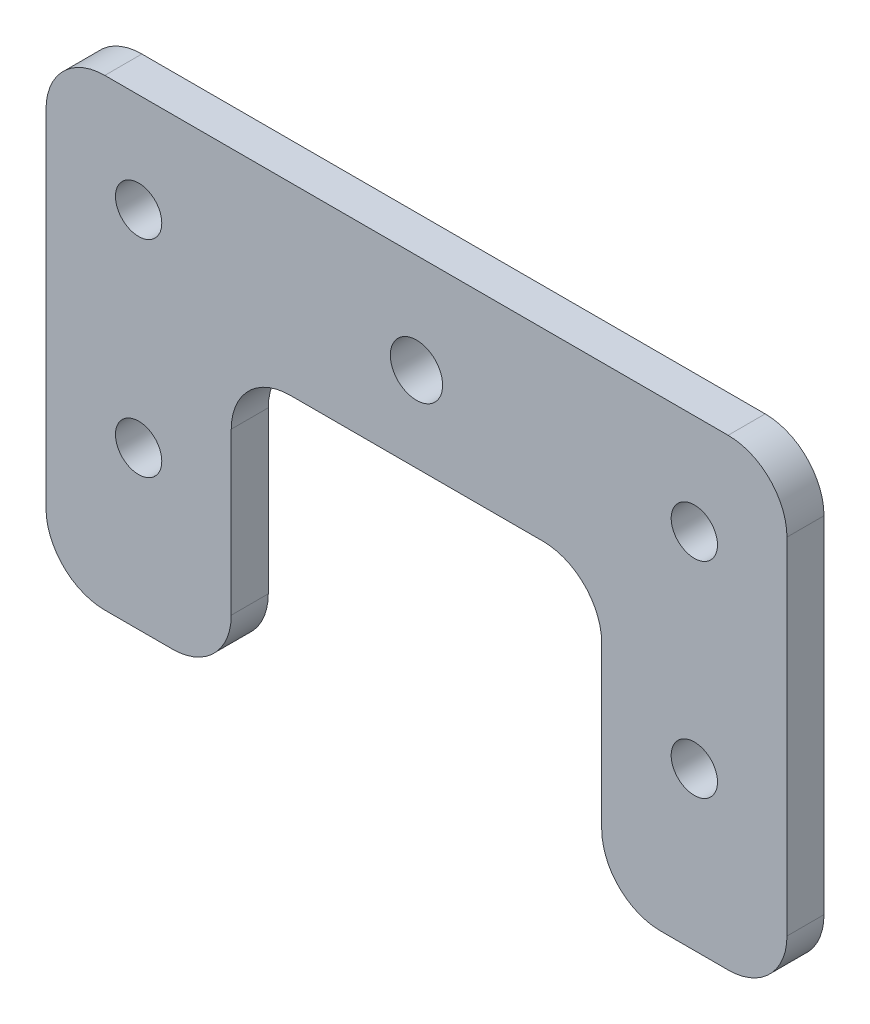
SolidWorks part; units mm, degrees
ref_plane "Alzado" through (0, 0, 0) normal (0, 0, 1) x (1, 0, 0)
ref_plane "Planta" through (0, 0, 0) normal (0, 1, 0) x (1, 0, 0)
ref_plane "Vista lateral" through (0, 0, 0) normal (1, 0, 0) x (0, 0, -1)
sketch "Croquis1" plane through (0, 0, 0) normal (0, 0, 1) x (1, 0, 0)
  line L1 (26.5381, 6.6994) -> (53.8381, 6.6994)
  line L2 (0.1881, 6.6044) -> (0.1881, 20.2544)
  line L3 (6.5381, 26.6044) -> (73.8381, 26.6044)
  line L4 (80.1881, 6.6044) -> (80.1881, 20.2544)
  line L6 (0.1881, 6.6044) -> (0.1881, -17.0456)
  line L7 (6.5381, -23.3956) -> (13.8381, -23.3956)
  line L8 (20.1881, 0.3494) -> (20.1881, -17.0456)
  line L13 (40.1881, 26.6044) -> (40.1881, -35.7819) construction
  line L14 (73.8381, -23.3956) -> (66.5381, -23.3956)
  line L15 (60.1881, 0.3494) -> (60.1881, -17.0456)
  line L16 (80.1881, 6.6044) -> (80.1881, -17.0456)
  circle A1 centre (10.1881, 15.8665) radius 2.5
  circle A2 centre (70.1881, 15.7714) radius 2.5
  circle A3 centre (10.1881, -6.3956) radius 2.5
  arc A5 (26.5381, 6.6994) -> (20.1881, 0.3494) centre (26.5381, 0.3494) ccw
  arc A6 (80.1881, 20.2544) -> (73.8381, 26.6044) centre (73.8381, 20.2544) ccw
  arc A7 (6.5381, 26.6044) -> (0.1881, 20.2544) centre (6.5381, 20.2544) ccw
  arc A8 (60.1881, 0.3494) -> (53.8381, 6.6994) centre (53.8381, 0.3494) ccw
  arc A9 (6.5381, -23.3956) -> (0.1881, -17.0456) centre (6.5381, -17.0456) cw
  arc A10 (13.8381, -23.3956) -> (20.1881, -17.0456) centre (13.8381, -17.0456) ccw
  circle A24 centre (40.1881, 15.8665) radius 2.8214
  arc A30 (73.8381, -23.3956) -> (80.1881, -17.0456) centre (73.8381, -17.0456) ccw
  arc A31 (66.5381, -23.3956) -> (60.1881, -17.0456) centre (66.5381, -17.0456) cw
  circle A32 centre (70.1881, -6.3956) radius 2.5
  point P22 (20.1881, 6.6994)
  point P25 (80.1881, 26.6044)
  point P28 (0.1881, 26.6044)
  point P31 (114.1981, 6.6994)
  point P34 (0.1881, -23.3956)
  point P37 (20.1881, -23.3956)
  dimension "D8" = 5
  dimension "D19" = 6.35
  dimension "D20" = 6.35
  dimension "D21" = 6.35
  dimension "D1" = 20
  dimension "D2" = 80
  dimension "D3" = 30
  dimension "D4" = 20
  dimension "D15" = 10
  dimension "D16" = 10
  dimension "D18" = 94.01
extrude "Saliente-Extruir1" add sketch "Croquis1" along normal blind 4
